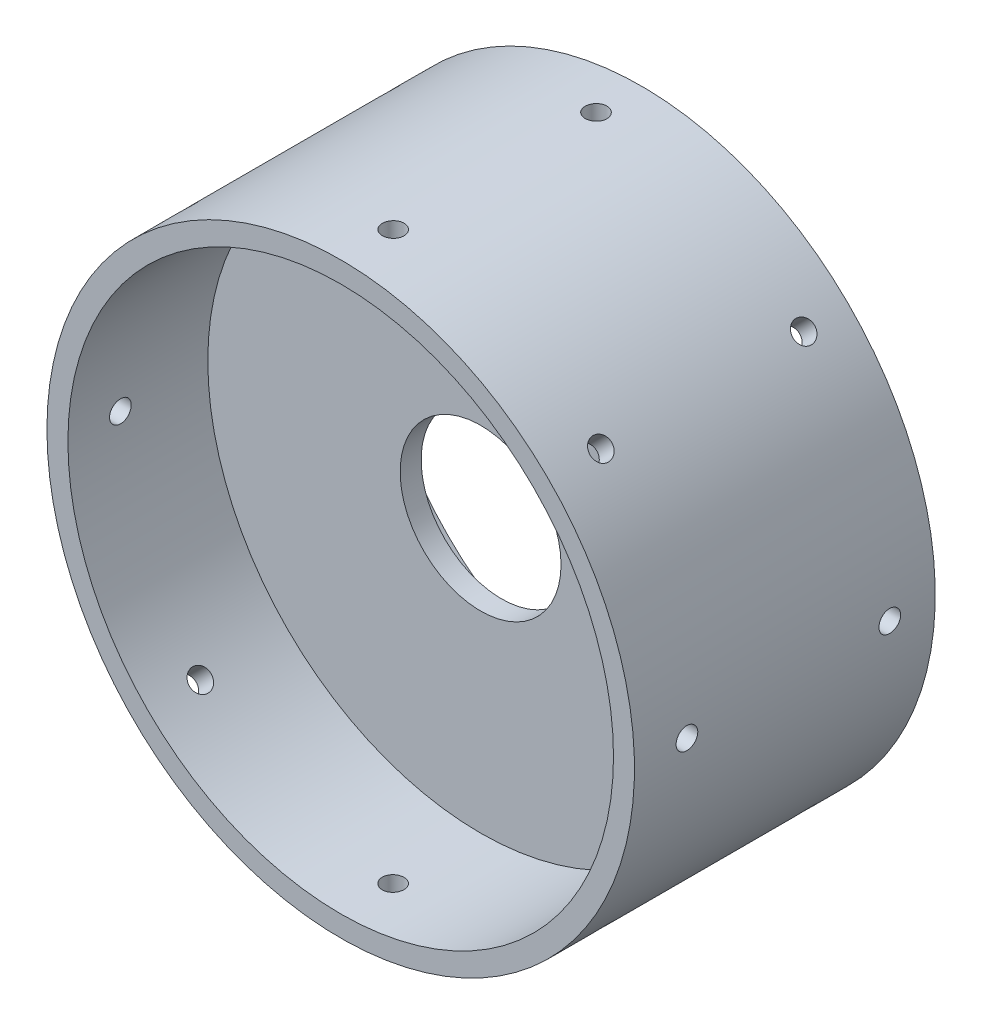
SolidWorks part; units mm, degrees
material "AISI 1020"
ref_plane "Plan de face" through (0, 0, 0) normal (0, 0, 1) x (1, 0, 0)
ref_plane "Plan de dessus" through (0, 0, 0) normal (0, 1, 0) x (1, 0, 0)
ref_plane "Plan de droite" through (0, 0, 0) normal (1, 0, 0) x (0, 0, -1)
sketch "Esquisse1" plane through (0, 0, 0) normal (0, 0, 1) x (1, 0, 0)
  circle A0 centre (0, 0) radius 42
  dimension "D1" = 84
extrude "Boss.-Extru.1" add sketch "Esquisse1" along normal blind 3
sketch "Esquisse5" plane through (0, 0, 0) normal (1, 0, 0) x (0, 0, -1)
  line L0 (-3, 42) -> (-23, 42)
  line L1 (-23, 42) -> (-23, 39)
  line L2 (-23, 39) -> (-3, 39)
  line L3 (-3, 39) -> (-3, 42)
  line L4 (0, 39) -> (20, 39)
  line L5 (20, 39) -> (20, 42)
  line L6 (0, 0) -> (-20.9637, 0) construction
  line L7 (20, 42) -> (0, 42)
  line L8 (0, 42) -> (0, 39)
  dimension "D1" = 20
  dimension "D2" = 3
  dimension "D3" = 20
revolve "Révolution1" add sketch "Esquisse5" angle 360 about L6
hole_wizard "Dégagement M2.51" positions "Esquisse3D1" profile "Esquisse6" hole size "M2.5" standard "ISO" end condition through all
sketch3d "Esquisse3D1"
  line L0 (0, 0, 23) -> (73.4921, 0, 23) construction
  line L1 (0, 0, 23) -> (0, 0, 3) construction
  line L5 (42, 0, 15.5) -> (42, 0, 23) construction
  line L6 (-0.4768, 0, -20) -> (62.7209, 0, -20) construction
  line L9 (42, 0, 3.7428) -> (42, 0, -20) construction
  circle A0 centre (0, 0, -20) radius 42 construction
  point P0 (42, 0, 15.5)
  point P21 (42, 0, -13.5)
  point P43 (0, 0, -62)
  dimension "D1" = 7.5
  dimension "D2" = 6.5
sketch "Esquisse6" plane through (42, 0, 15.5) normal (0, 1, 0) x (0, 0, -1)
  line L0 (0, 0) -> (0, 101.397)
  line L1 (0, 101.397) -> (1.55, 101.397)
  line L2 (1.55, 101.397) -> (1.55, 0)
  line L5 (1.55, 0) -> (0, 0)
  line L11 (0, -6.35) -> (0, 107.95) construction
  dimension "Diamètre du perçage jusqu'au prochain" = 3.1
  dimension "Profondeur du perçage jusqu'au prochain" = 101.397
pattern_circular "Répétition circulaire1" count 8 over 360 about axis through (0, 0, 0) along (0, 0, -1) of "Dégagement M2.51"
sketch "Esquisse7" plane through (0, 0, 0) normal (0, 0, -1) x (-1, 0, 0)
  circle A0 centre (0, 0) radius 10.4
  dimension "D1" = 20.8
split line "Ligne de séparation1"
sketch "Esquisse8" plane through (0, 0, 3) normal (0, 0, 1) x (1, 0, 0)
  circle A0 centre (0, 0) radius 11.5
  dimension "D1" = 23
extrude "Enlèv. mat.-Extru.1" cut sketch "Esquisse8" against normal blind 10
sketch "Esquisse11" plane through (0, 0, 0) normal (0, 0, 1) x (1, 0, 0)
  circle A0 centre (0, 0) radius 21.0433
  circle A1 centre (0, 0) radius 11.5
split line "Ligne de séparation2"
